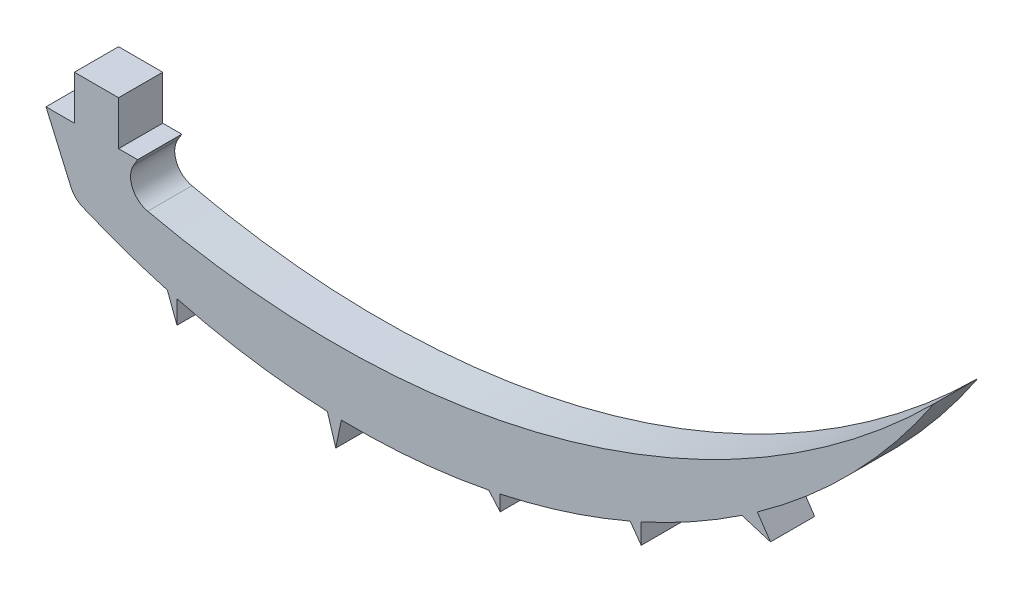
SolidWorks part; units mm, degrees
ref_plane "Front Plane" through (0, 0, 0) normal (0, 0, 1) x (1, 0, 0)
ref_plane "Top Plane" through (0, 0, 0) normal (0, 1, 0) x (1, 0, 0)
ref_plane "Right Plane" through (0, 0, 0) normal (1, 0, 0) x (0, 0, -1)
sketch "Sketch1" plane through (0, 0, 0) normal (0, 0, 1) x (1, 0, 0)
  line L0 (6.4335, 1.524) -> (4.9095, 1.524)
  line L1 (4.9095, 1.524) -> (6.4335, 1.524) construction
  line L2 (4.9095, 1.524) -> (4.9095, 0)
  line L3 (4.9095, 0) -> (3.9298, 0)
  line L4 (6.4335, 1.524) -> (6.4335, 0)
  line L5 (6.4335, 0) -> (7.091, 0)
  line L6 (7.091, 0) -> (6.4335, -1.1176)
  line L7 (3.9298, 0) -> (4.9095, -2.2408)
  line L8 (8.1171, -3.3857) -> (8.4499, -4.2682)
  line L9 (8.4499, -4.2682) -> (8.4499, -3.4759)
  line L10 (13.6386, -4.2502) -> (13.928, -5.2002)
  line L11 (13.928, -5.2002) -> (14.1218, -4.2641)
  line L12 (19.2073, -3.8162) -> (19.6021, -4.2682)
  line L13 (19.6021, -4.2682) -> (19.6021, -3.7351)
  line L14 (24.0862, -2.3027) -> (24.4685, -2.8346)
  line L15 (24.4685, -2.8346) -> (24.4685, -2.1338)
  line L16 (27.941, -0.2027) -> (28.9293, -0.5027)
  line L17 (28.9293, -0.5027) -> (28.4747, 0.1654)
  arc A0 (6.4335, -1.1176) -> (34.5647, 6.4394) centre (13.928, 27.1218) ccw
  arc A1 (34.5647, 6.4394) -> (28.4747, 0.1654) centre (14.5688, 19.7561) cw
  arc A2 (27.941, -0.2027) -> (24.4685, -2.1338) centre (14.5688, 19.7561) cw
  arc A3 (24.0862, -2.3027) -> (19.6021, -3.7351) centre (14.5688, 19.7561) cw
  arc A4 (19.2073, -3.8162) -> (14.1218, -4.2641) centre (14.5688, 19.7561) cw
  arc A5 (13.6386, -4.2502) -> (8.4499, -3.4759) centre (14.5688, 19.7561) cw
  arc A6 (8.1171, -3.3857) -> (4.9095, -2.2408) centre (14.5688, 19.7561) cw
extrude "Boss-Extrude1" add sketch "Sketch1" along normal blind 1.524
fillet "Fillet1" radius 0.762 1 edges at (6.4335, -1.1176, 0.762)
fillet "Fillet2" radius 0.762 1 edges at (4.9095, -2.2408, 0.762)
